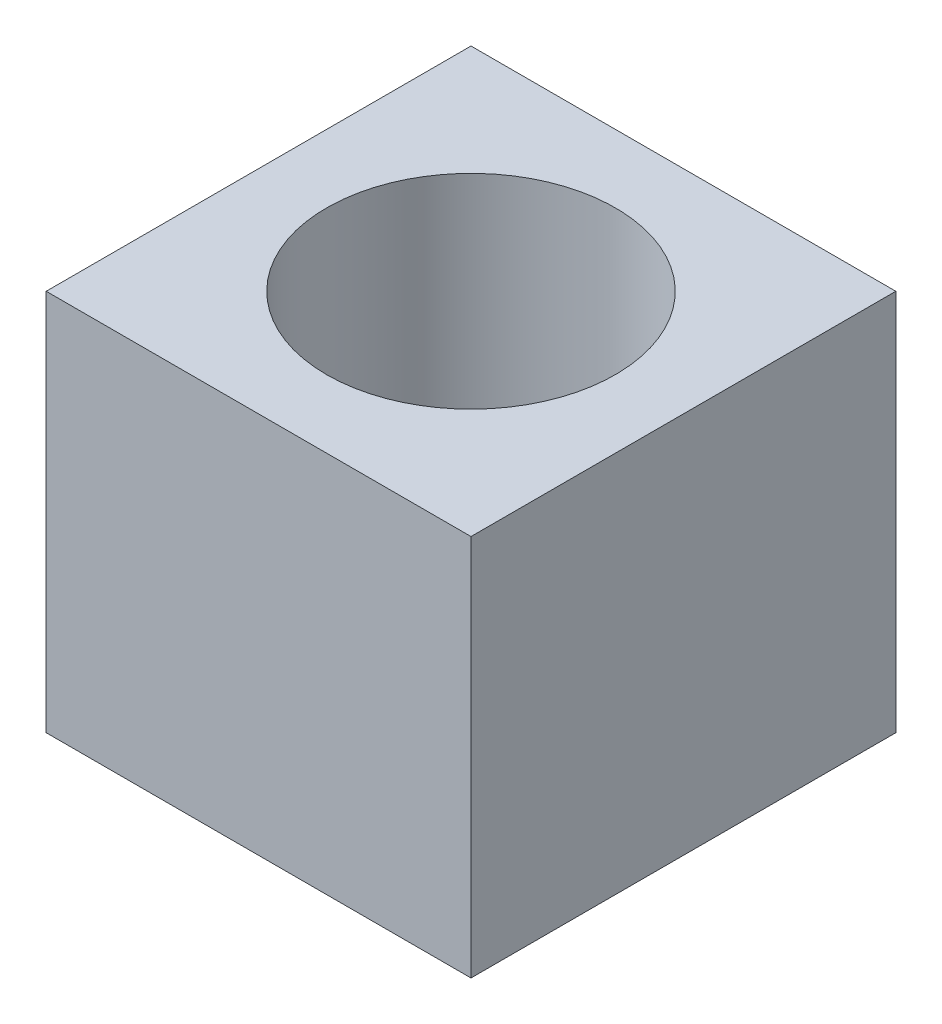
SolidWorks part; units mm, degrees
ref_plane "Front Plane" through (0, 0, 0) normal (0, 0, 1) x (1, 0, 0)
ref_plane "Top Plane" through (0, 0, 0) normal (0, 1, 0) x (1, 0, 0)
ref_plane "Right Plane" through (0, 0, 0) normal (1, 0, 0) x (0, 0, -1)
sketch "Sketch1" plane through (0, 0, 0) normal (0, 1, 0) x (1, 0, 0)
  line L1 (-2.5, -2.5) -> (2.5, -2.5)
  line L2 (-2.5, -2.5) -> (-2.5, 2.5)
  line L3 (-2.5, 2.5) -> (2.5, 2.5)
  line L4 (2.5, -2.5) -> (2.5, 2.5)
  line L5 (-2.5, -2.5) -> (2.5, 2.5) construction
  line L6 (-2.5, 2.5) -> (2.5, -2.5) construction
  circle A0 centre (0, 0) radius 1.7
  dimension "D1" = 3.4
  dimension "D2" = 5
extrude "Boss-Extrude1" add sketch "Sketch1" along normal blind 4.5
